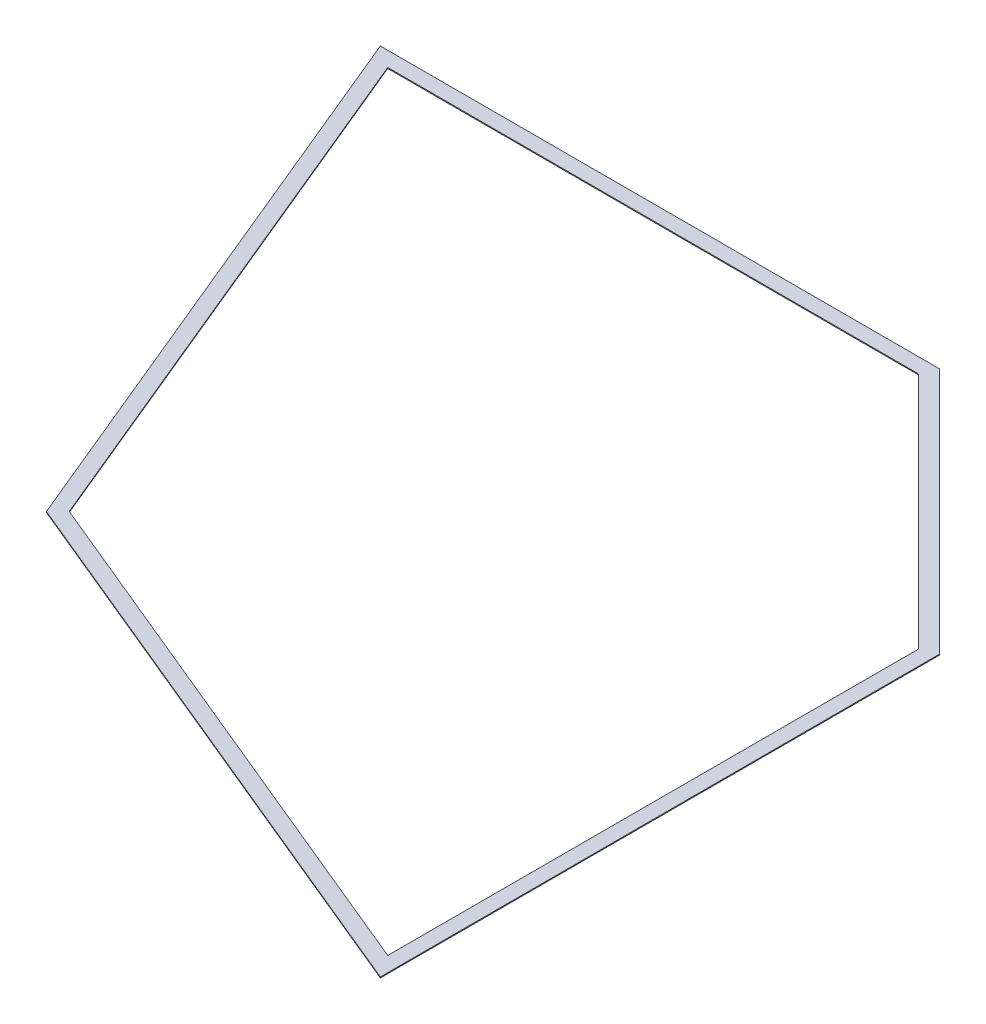
SolidWorks part; units mm, degrees
ref_plane "Front Plane" through (0, 0, 0) normal (0, 0, 1) x (1, 0, 0)
ref_plane "Top Plane" through (0, 0, 0) normal (0, 1, 0) x (1, 0, 0)
ref_plane "Right Plane" through (0, 0, 0) normal (1, 0, 0) x (0, 0, -1)
sketch "Sketch1" plane through (0, 0, 0) normal (0, 1, 0) x (1, 0, 0)
  line L0 (-3013.894, 0) -> (0, 0) construction
  line L1 (0, 0) -> (0, -3013.894) construction
  line L2 (-1029.4997, -187.325) -> (-187.325, -1029.4997)
  line L3 (-187.325, -1029.4997) -> (-187.325, -2936.3015)
  line L4 (-187.325, -2936.3015) -> (-2131.1449, -2131.1449)
  line L5 (-2131.1449, -2131.1449) -> (-2936.3015, -187.325)
  line L6 (-2936.3015, -187.325) -> (-1029.4997, -187.325)
  line L7 (-238.125, -1050.5418) -> (-238.125, -2860.2739)
  line L8 (-238.125, -2860.2739) -> (-2092.2643, -2092.2643)
  line L9 (-2092.2643, -2092.2643) -> (-2860.2739, -238.125)
  line L10 (-2860.2739, -238.125) -> (-1050.5418, -238.125)
  line L11 (-1050.5418, -238.125) -> (-238.125, -1050.5418)
  line L12 (-2131.1449, -2131.1449) -> (0, 0) construction
  dimension "D1" = 3013.894
  dimension "D2" = 45
  dimension "D3" = 860.425
  dimension "D4" = 187.325
  dimension "D5" = 135
  dimension "D7" = 187.325
  dimension "D6" = 50.8
extrude "Boss-Extrude1" add sketch "Sketch1" along normal blind 3.175
